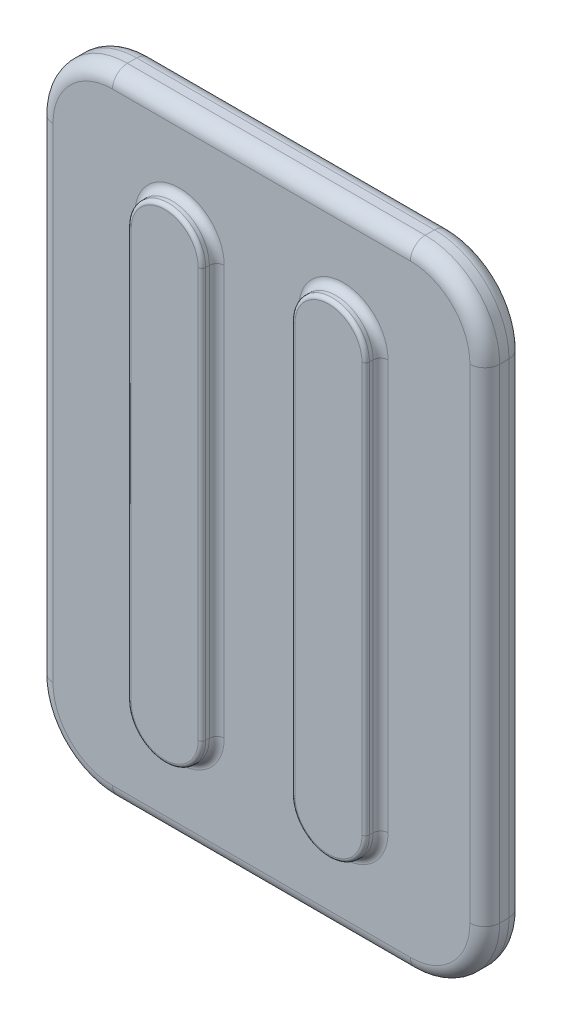
SolidWorks part; units mm, degrees
ref_plane "前视基准面" through (0, 0, 0) normal (0, 0, 1) x (1, 0, 0)
ref_plane "上视基准面" through (0, 0, 0) normal (0, 1, 0) x (1, 0, 0)
ref_plane "右视基准面" through (0, 0, 0) normal (1, 0, 0) x (0, 0, -1)
sketch "草图1" plane through (0, 0, 0) normal (0, 0, 1) x (1, 0, 0)
  line L1 (-300, 425) -> (300, 425)
  line L2 (-300, 425) -> (-300, -425)
  line L3 (-300, -425) -> (300, -425)
  line L4 (300, 425) -> (300, -425)
  line L5 (-300, 425) -> (300, -425) construction
  line L6 (-300, -425) -> (300, 425) construction
  point P0 (0, 0)
  dimension "D1" = 600
  dimension "D2" = 850
extrude "凸台-拉伸1" add sketch "草图1" along normal blind 52.4849
sketch "草图2" plane through (0, 0, 52.4849) normal (0, 0, 1) x (1, 0, 0)
  line L0 (0, 425) -> (0, -425) construction
  line L1 (300, 425) -> (-300, 425) construction
  line L2 (-300, -425) -> (300, -425) construction
  line L3 (-110, 275) -> (-110, -275) construction
  line L4 (-60, 275) -> (-60, -275)
  line L5 (-160, 275) -> (-160, -275)
  line L6 (110, 275) -> (110, -275) construction
  line L7 (60, 275) -> (60, -275)
  line L8 (160, 275) -> (160, -275)
  arc A0 (-60, 275) -> (-160, 275) centre (-110, 275) ccw
  arc A1 (-160, -275) -> (-60, -275) centre (-110, -275) ccw
  arc A2 (60, 275) -> (160, 275) centre (110, 275) cw
  arc A3 (160, -275) -> (60, -275) centre (110, -275) cw
  point P8 (-110, 0)
  point P16 (110, 0)
  dimension "D2" = 50
  dimension "D1" = 550
  dimension "D3" = 110
extrude "凸台-拉伸2" add sketch "草图2" along normal blind 20
fillet "圆角1" radius 100 4 edges at (300, 425, 26.2425) (-300, 425, 26.2425) (300, -425, 26.2425) (-300, -425, 26.2425)
fillet "圆角2" radius 10 8 edges at (110, 325, 52.4849) (160, 0, 52.4849) (110, -325, 52.4849) (-110, 325, 52.4849) (-60, 0, 52.4849) (-110, -325, 52.4849) (60, 0, 52.4849) (-160, 0, 52.4849)
fillet "圆角3" radius 5 8 edges at (-60, 0, 72.4849) (-110, -325, 72.4849) (-160, 0, 72.4849) (-110, 325, 72.4849) (160, 0, 72.4849) (110, -325, 72.4849) (60, 0, 72.4849) (110, 325, 72.4849)
fillet "圆角4" radius 20 16 edges at (-270.7107, 395.7107, 0) (0, 425, 0) (270.7107, 395.7107, 0) (300, 0, 0) (270.7107, -395.7107, 0) (0, -425, 0) (-270.7107, -395.7107, 0) (-270.7107, 395.7107, 52.4849) (0, 425, 52.4849) (270.7107, 395.7107, 52.4849) (300, 0, 52.4849) (270.7107, -395.7107, 52.4849) (0, -425, 52.4849) (-270.7107, -395.7107, 52.4849) (-300, 0, 0) (-300, 0, 52.4849)
sketch "草图3" plane through (0, 425, 0) normal (0, 1, 0) x (1, 0, 0)
  line L0 (0, 0) -> (0, 122.9159) construction
  line L1 (-159.75, 0) -> (-110.25, 0)
  line L2 (-200, 0) -> (-280, 0) construction
  line L3 (200, 0) -> (-200, 0) construction
  line L4 (-110.25, 0) -> (-110.25, 7.38)
  line L5 (-110.25, 7.38) -> (-122.225, 19.39)
  line L6 (-122.225, 19.39) -> (-147.775, 19.39)
  line L7 (-135, 0) -> (-135, 19.39) construction
  line L8 (-159.75, 7.38) -> (-147.775, 19.39)
  line L9 (-159.75, 0) -> (-159.75, 7.38)
  line L10 (135, 0) -> (135, 19.39) construction
  line L11 (159.75, 0) -> (159.75, 7.38)
  line L12 (159.75, 7.38) -> (147.775, 19.39)
  line L13 (122.225, 19.39) -> (147.775, 19.39)
  line L14 (110.25, 7.38) -> (122.225, 19.39)
  line L15 (110.25, 0) -> (110.25, 7.38)
  line L16 (159.75, 0) -> (110.25, 0)
  dimension "D1" = 49.5
  dimension "D2" = 25.55
  dimension "D3" = 7.38
  dimension "D4" = 19.39
  dimension "D5" = 220.5
extrude "凸台-拉伸3" add sketch "草图3" against normal blind 670 from offset 100 offset against normal yes
scale "缩放比例1" scale about centroid uniform scaling yes scale factor 0.111111
